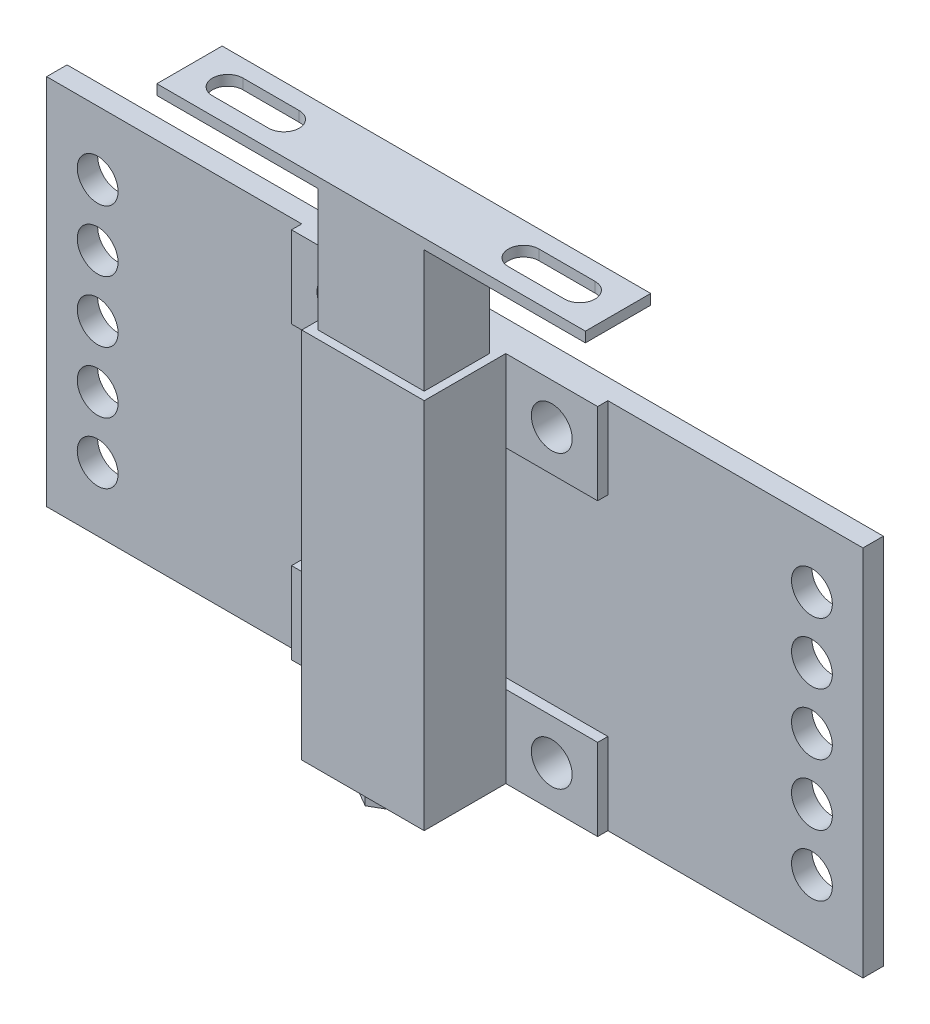
SolidWorks part; units mm, degrees
ref_plane "Front Plane" through (0, 0, 0) normal (0, 0, 1) x (1, 0, 0)
ref_plane "Top Plane" through (0, 0, 0) normal (0, 1, 0) x (1, 0, 0)
ref_plane "Right Plane" through (0, 0, 0) normal (1, 0, 0) x (0, 0, -1)
sketch "Sketch1" plane through (0, 0, 0) normal (0, 0, 1) x (1, 0, 0)
  line L0 (33.3375, -45.2437) -> (-33.3375, 45.2437) construction
  line L1 (-33.3375, 45.2437) -> (33.3375, 45.2437)
  line L2 (-33.3375, 45.2437) -> (-33.3375, -45.2437)
  line L3 (-33.3375, -45.2437) -> (33.3375, -45.2437)
  line L4 (33.3375, 45.2437) -> (33.3375, -45.2437)
  dimension "D1" = 66.675
  dimension "D2" = 90.4875
sketch "Sketch2" plane through (0, 0, 0) normal (0, 0, 1) x (1, 0, 0)
  line L0 (0, 0) -> (-33.3375, 0) construction
  line L1 (-47.625, -32.5437) -> (47.625, -32.5437)
  line L2 (-47.625, -32.5437) -> (-47.625, -57.9437)
  line L3 (-47.625, -57.9437) -> (47.625, -57.9437)
  line L4 (47.625, -32.5437) -> (47.625, -57.9437)
  line L5 (-33.3375, 45.2437) -> (-33.3375, -45.2437) construction
  line L6 (-47.625, -45.2437) -> (-33.3375, -45.2437) construction
  line L7 (0, -32.5438) -> (0, -45.2437) construction
  line L8 (-33.3375, -45.2437) -> (33.3375, -45.2437) construction
  line L9 (0, 32.5438) -> (0, 45.2437) construction
  line L10 (-47.625, 45.2437) -> (-33.3375, 45.2437) construction
  line L11 (47.625, 32.5437) -> (47.625, 57.9437)
  line L12 (-47.625, 57.9437) -> (47.625, 57.9437)
  line L13 (-47.625, 32.5437) -> (-47.625, 57.9437)
  line L14 (-47.625, 32.5437) -> (47.625, 32.5437)
  circle A0 centre (-33.3375, -45.2437) radius 6.35
  circle A1 centre (33.3375, -45.2437) radius 6.35
  circle A2 centre (33.3375, 45.2437) radius 6.35
  circle A3 centre (-33.3375, 45.2437) radius 6.35
  dimension "D1" = 12.7
  dimension "D2" = 95.25
  dimension "D3" = 25.4
extrude "Extrude1" add sketch "Sketch2" along normal blind 3.175
sketch "Sketch3" plane through (0, 0, 3.175) normal (0, 0, 1) x (1, 0, 0)
  line L0 (47.625, 57.9437) -> (-47.625, 57.9437) construction
  line L1 (-19.05, 57.9437) -> (19.05, 57.9437)
  line L2 (-19.05, 57.9437) -> (-19.05, -57.9437)
  line L3 (-19.05, -57.9437) -> (19.05, -57.9437)
  line L4 (19.05, 57.9437) -> (19.05, -57.9437)
  line L5 (-47.625, -57.9437) -> (47.625, -57.9437) construction
  line L6 (-19.05, 57.9437) -> (19.05, -57.9437) construction
  dimension "D1" = 38.1
extrude "Extrude2" add sketch "Sketch3" along normal blind 25.4
sketch "Sketch4" plane through (0, 57.9437, 0) normal (0, 1, 0) x (1, 0, 0)
  line L8 (16.51, -26.035) -> (16.51, -5.715)
  line L9 (-16.51, -26.035) -> (16.51, -26.035)
  line L10 (-16.51, -5.715) -> (-16.51, -26.035)
  line L11 (16.51, -5.715) -> (-16.51, -5.715)
  line L12 (16.51, -26.035) -> (16.51, -5.715)
  line L13 (-16.51, -26.035) -> (16.51, -26.035)
  line L14 (-16.51, -5.715) -> (-16.51, -26.035)
  line L15 (16.51, -5.715) -> (-16.51, -5.715)
  dimension "D1" = 2.54
extrude "Extrude3" add sketch "Sketch4" along normal blind 38.1
sketch "Sketch5" plane through (0, 96.0437, 0) normal (0, 1, 0) x (1, 0, 0)
  line L0 (-16.51, -26.035) -> (16.51, -26.035) construction
  line L1 (-66.675, -5.715) -> (66.675, -5.715)
  line L2 (-66.675, -5.715) -> (-66.675, -26.035)
  line L3 (-66.675, -26.035) -> (66.675, -26.035)
  line L4 (66.675, -5.715) -> (66.675, -26.035)
  line L5 (0, 0) -> (0, -26.035) construction
  line L6 (16.51, -5.715) -> (-16.51, -5.715) construction
  dimension "D1" = 133.35
extrude "Extrude4" add sketch "Sketch5" along normal blind 3.175
sketch "Sketch6" plane through (0, 99.2187, 0) normal (0, 1, 0) x (1, 0, 0)
  line L0 (0, 0) -> (0, -32.2096) construction
  line L1 (-54.7687, -15.875) -> (-66.675, -15.875) construction
  line L3 (-66.675, -5.715) -> (-66.675, -26.035) construction
  line L4 (54.7688, -20.6375) -> (37.3063, -20.6375)
  line L5 (-54.7687, -15.875) -> (-37.3062, -15.875) construction
  line L6 (54.7688, -11.1125) -> (37.3063, -11.1125)
  line L10 (-54.7688, -11.1125) -> (-37.3063, -11.1125)
  line L13 (-54.7688, -20.6375) -> (-37.3063, -20.6375)
  arc A0 (-54.7688, -11.1125) -> (-54.7688, -20.6375) centre (-54.7687, -15.875) ccw
  arc A1 (-37.3063, -20.6375) -> (-37.3063, -11.1125) centre (-37.3062, -15.875) ccw
  arc A2 (37.3063, -20.6375) -> (37.3063, -11.1125) centre (37.3062, -15.875) cw
  arc A3 (54.7688, -11.1125) -> (54.7688, -20.6375) centre (54.7687, -15.875) cw
  dimension "D1" = 9.525
  dimension "D2" = 109.5375
  dimension "D3" = 74.6125
extrude "Cut-Extrude1" cut sketch "Sketch6" against normal through all
sketch "Sketch8" plane through (0, -57.9437, 0) normal (0, -1, 0) x (1, 0, 0)
  line L0 (0, 0) -> (0, 13.9315) construction
  line L1 (12.065, 6.9657) -> (12.065, 20.8972)
  line L2 (12.065, 20.8972) -> (0, 27.8629)
  line L3 (0, 27.8629) -> (-12.065, 20.8972)
  line L4 (-12.065, 20.8972) -> (-12.065, 6.9657)
  line L5 (-12.065, 6.9657) -> (0, 0)
  line L6 (0, 0) -> (12.065, 6.9657)
  circle A0 centre (0, 13.9315) radius 12.065 construction
  dimension "D1" = 24.13
extrude "Extrude5" add sketch "Sketch8" along normal blind 3.175
sketch "Sketch9" plane through (0, -61.1187, 0) normal (0, -1, 0) x (1, 0, 0)
  line L0 (0, 13.9315) -> (0, 0) construction
  circle A0 centre (0, 13.9315) radius 6.35
  circle A1 centre (0, 13.9315) radius 12.065 construction
  dimension "D1" = 12.7
extrude "Extrude6" add sketch "Sketch9" along normal blind 3.175
sketch "Sketch10" plane through (0, 0, 0) normal (0, 0, -1) x (-1, 0, 0)
  line L0 (0, 0) -> (0, -57.9437) construction
  line L1 (-127, 57.9437) -> (127, 57.9438)
  line L2 (-127, 57.9437) -> (-127, -57.9437)
  line L3 (-127, -57.9437) -> (127, -57.9437)
  line L4 (127, 57.9438) -> (127, -57.9437)
  line L5 (-47.625, 57.9437) -> (47.625, 57.9437) construction
  line L6 (0, -57.9437) -> (-47.625, -57.9437) construction
  dimension "D1" = 254
extrude "Extrude7" add sketch "Sketch10" along normal blind 6.35
sketch "Sketch11" plane through (0, 0, 0) normal (0, 0, 1) x (1, 0, 0)
  circle A0 centre (33.3375, -45.2437) radius 6.35 construction
  circle A1 centre (-33.3375, -45.2437) radius 6.35 construction
  circle A2 centre (-33.3375, 45.2437) radius 6.35 construction
  circle A3 centre (33.3375, 45.2437) radius 6.35 construction
  circle A4 centre (33.3375, -45.2437) radius 6.35
  circle A5 centre (-33.3375, -45.2437) radius 6.35
  circle A6 centre (-33.3375, 45.2437) radius 6.35
  circle A7 centre (33.3375, 45.2437) radius 6.35
extrude "Cut-Extrude2" cut sketch "Sketch11" against normal through all
sketch "Sketch12" plane through (0, 0, -6.35) normal (0, 0, -1) x (-1, 0, 0)
  line L0 (0, 57.9437) -> (0, -41.4657) construction
  line L1 (-16.51, 57.9437) -> (16.51, 57.9437) construction
  line L2 (-127, 57.9437) -> (-127, -57.9437) construction
  line L3 (0, 0) -> (-111.125, 0) construction
  circle A0 centre (-111.125, 0) radius 6.35
  circle A1 centre (111.125, 0) radius 6.35
  dimension "D2" = 12.7
  dimension "D1" = 15.875
extrude "Cut-Extrude3" cut sketch "Sketch12" against normal through all
pattern_linear "LPattern1" count 3 spacing 19.05 along (0, 1, 0) count 3 spacing 19.05 along (0, -1, 0) of "Cut-Extrude3"
